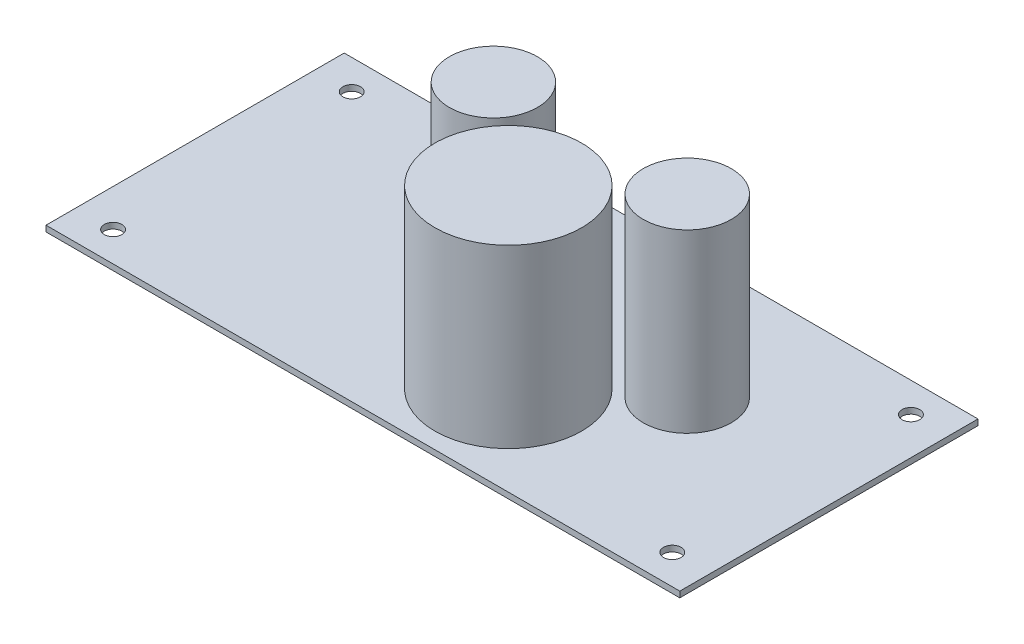
SolidWorks part; units mm, degrees
material "A-Fibra di vetro"
ref_plane "Front Plane" through (0, 0, 0) normal (0, 0, 1) x (1, 0, 0)
ref_plane "Top Plane" through (0, 0, 0) normal (0, 1, 0) x (1, 0, 0)
ref_plane "Right Plane" through (0, 0, 0) normal (1, 0, 0) x (0, 0, -1)
sketch "Schizzo1" plane through (0, 0, 0) normal (0, 1, 0) x (1, 0, 0)
  line L0 (-53.975, 25.395) -> (53.975, -25.395) construction
  line L1 (-53.975, 25.395) -> (53.975, 25.395)
  line L2 (-53.975, 25.395) -> (-53.975, -25.395)
  line L3 (-53.975, -25.395) -> (53.975, -25.395)
  line L4 (53.975, 25.395) -> (53.975, -25.395)
  line L5 (47.625, 20.32) -> (-47.625, -20.32) construction
  line L6 (-47.625, 20.32) -> (47.625, 20.32) construction
  line L7 (-47.625, 20.32) -> (-47.625, -20.32) construction
  line L8 (-47.625, -20.32) -> (47.625, -20.32) construction
  line L9 (47.625, 20.32) -> (47.625, -20.32) construction
  point P4 (0, 0)
  point P10 (0, 0)
  dimension "D1" = 107.95
  dimension "D2" = 50.79
  dimension "D3" = 95.25
  dimension "D4" = 40.64
extrude "Estrusione-Estrusione1" add sketch "Schizzo1" along normal blind 1
sketch "Schizzo2" plane through (0, 1, 0) normal (0, 1, 0) x (1, 0, 0)
  circle A0 centre (-47.625, 20.32) radius 1.5
  circle A1 centre (47.625, 20.32) radius 1.5
  circle A2 centre (47.625, -20.32) radius 1.5
  circle A3 centre (-47.625, -20.32) radius 1.5
  dimension "D1" = 3
extrude "Taglio-Estrusione1" cut sketch "Schizzo2" against normal through all
sketch "Schizzo3" plane through (0, 1, 0) normal (0, 1, 0) x (1, 0, 0)
  line L0 (53.975, 25.395) -> (53.975, -25.395) construction
  line L6 (-53.975, -25.395) -> (53.975, -25.395) construction
  line L7 (26.035, 3.815) -> (-6.985, 3.815) construction
  line L8 (9.525, 3.815) -> (9.525, -25.395) construction
  circle A0 centre (26.035, 3.815) radius 7.5
  circle A1 centre (-6.985, 3.815) radius 7.5
  circle A2 centre (9.525, -10.155) radius 12.5
  dimension "D1" = 27.94
  dimension "D4" = 15.24
  dimension "D5" = 15
  dimension "D6" = 15
  dimension "D7" = 25
  dimension "D2" = 29.21
  dimension "D3" = 33.02
extrude "Estrusione-Estrusione2" add sketch "Schizzo3" along normal blind 30
